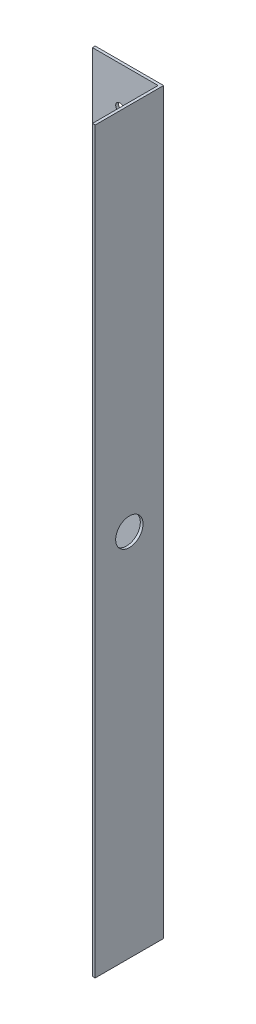
SolidWorks part; units mm, degrees
material "Aleación 1060"
ref_plane "Alzado" through (0, 0, 0) normal (0, 0, 1) x (1, 0, 0)
ref_plane "Planta" through (0, 0, 0) normal (0, 1, 0) x (1, 0, 0)
ref_plane "Vista lateral" through (0, 0, 0) normal (1, 0, 0) x (0, 0, -1)
sketch "Croquis1" plane through (0, 0, 0) normal (0, 0, 1) x (1, 0, 0)
  line L1 (-53.4017, 26.4852) -> (-29.4017, 26.4852)
  line L2 (-53.4017, 26.4852) -> (-53.4017, -243.5148)
  line L3 (-53.4017, -243.5148) -> (-29.4017, -243.5148)
  line L4 (-29.4017, 26.4852) -> (-29.4017, -243.5148)
  circle A0 centre (-43.4017, 12.4852) radius 1.5
  circle A1 centre (-43.4017, -229.5148) radius 1.5
  dimension "D6" = 10
  dimension "D1" = 24
  dimension "D2" = 270
  dimension "D3" = 14
  dimension "D4" = 14
  dimension "D5" = 10
sketch "Croquis2" plane through (0, 0, 0) normal (0, 0, 1) x (1, 0, 0)
  line L0 (-53.4017, -243.5148) -> (-29.4017, -243.5148) construction
  line L1 (-29.4017, 26.4852) -> (-28.4017, 26.4852)
  line L2 (-29.4017, 26.4852) -> (-29.4017, -243.5148)
  line L3 (-29.4017, -243.5148) -> (-28.4017, -243.5148)
  line L4 (-28.4017, 26.4852) -> (-28.4017, -243.5148)
  dimension "D1" = 1
extrude "Saliente-Extruir1" add sketch "Croquis1" along normal blind 1
extrude "Saliente-Extruir2" add sketch "Croquis2" along normal blind 25
sketch "Croquis3" plane through (-28.4017, 0, 0) normal (1, 0, 0) x (0, 0, -1)
  line L0 (0, -243.5148) -> (0, 26.4852) construction
  line L1 (-25, 26.4852) -> (0, 26.4852) construction
  circle A0 centre (-12.5, -108.5148) radius 5
  dimension "D1" = 12.5
  dimension "D2" = 135
extrude "Cortar-Extruir1" cut sketch "Croquis3" against normal blind 1
